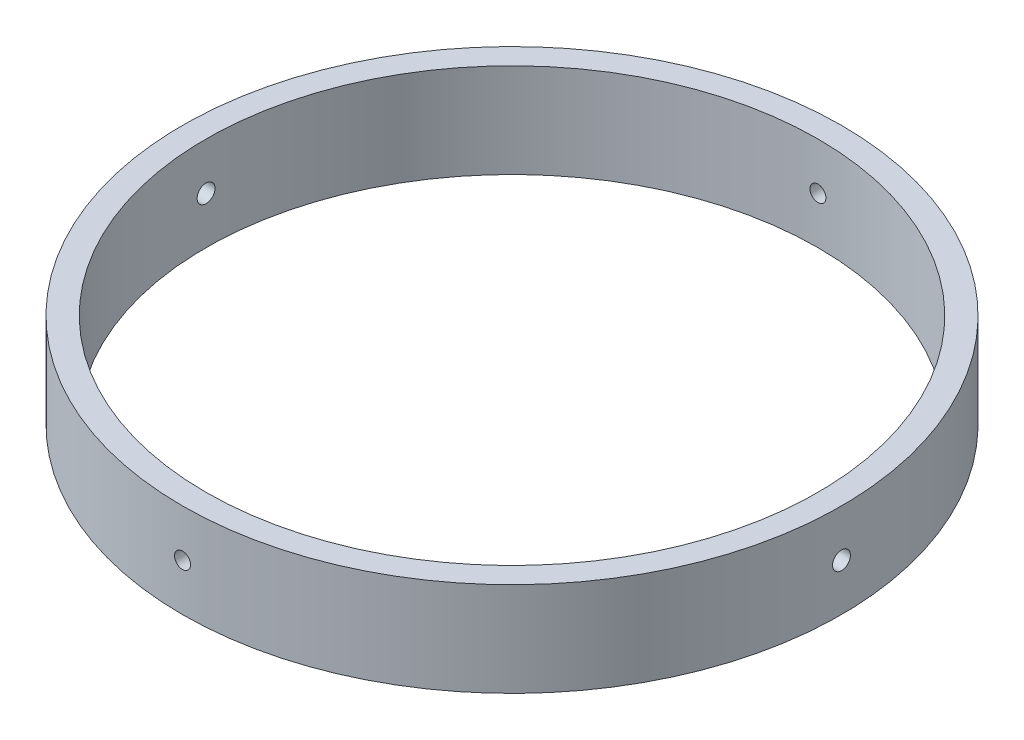
SolidWorks part; units mm, degrees
ref_plane "Front Plane" through (0, 0, 0) normal (0, 0, 1) x (1, 0, 0)
ref_plane "Top Plane" through (0, 0, 0) normal (0, 1, 0) x (1, 0, 0)
ref_plane "Right Plane" through (0, 0, 0) normal (1, 0, 0) x (0, 0, -1)
sketch "Sketch1" plane through (0, 0, 0) normal (0, 1, 0) x (1, 0, 0)
  circle A0 centre (0, 0) radius 88.9
  circle A1 centre (0, 0) radius 82.55
  dimension "D1" = 177.8
  dimension "D2" = 165.1
extrude "Boss-Extrude1" add sketch "Sketch1" along normal blind 25.4
sketch "Sketch2" plane through (0, 0, 0) normal (1, 0, 0) x (0, 0, -1)
  circle A0 centre (0, 12.7) radius 2.413
  dimension "D1" = 4.826
extrude "Cut-Extrude1" cut sketch "Sketch2" against normal through all and the other way through all
sketch "Sketch3" plane through (0, 0, 0) normal (0, 0, 1) x (1, 0, 0)
  circle A0 centre (0, 12.7) radius 2.159
  dimension "D1" = 4.318
extrude "Cut-Extrude2" cut sketch "Sketch3" against normal through all and the other way through all
